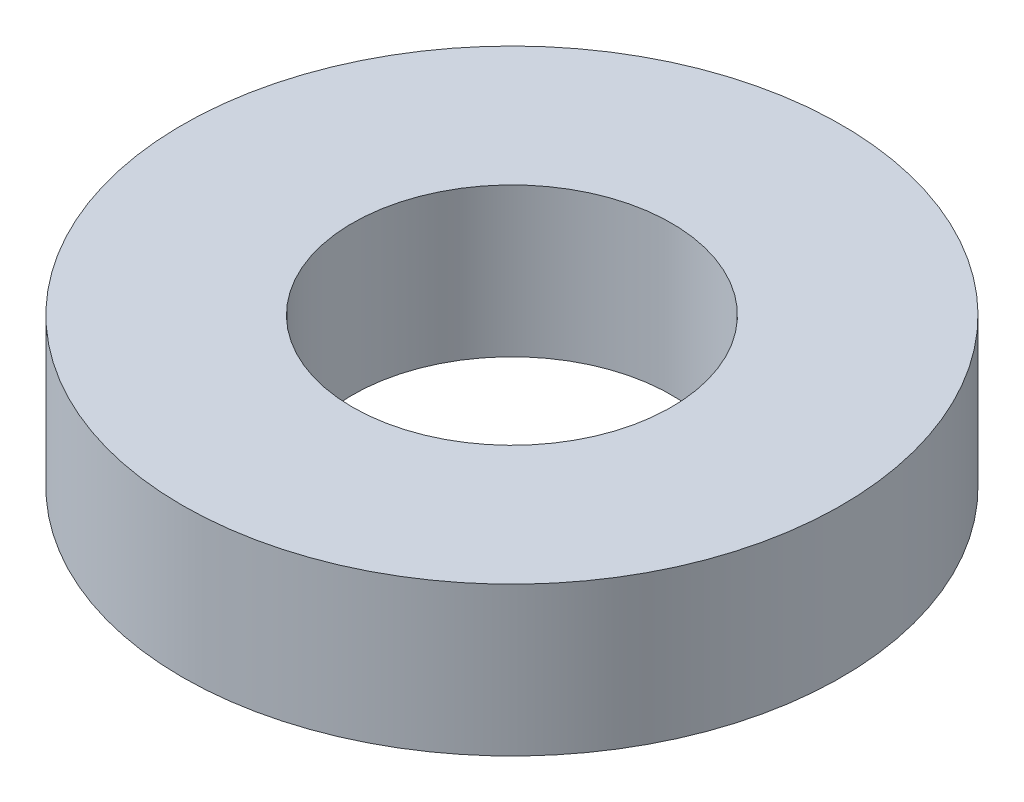
SolidWorks part; units mm, degrees
ref_plane "Front Plane" through (0, 0, 0) normal (0, 0, 1) x (1, 0, 0)
ref_plane "Top Plane" through (0, 0, 0) normal (0, 1, 0) x (1, 0, 0)
ref_plane "Right Plane" through (0, 0, 0) normal (1, 0, 0) x (0, 0, -1)
sketch "Sketch1" plane through (0, 0, 0) normal (0, 1, 0) x (1, 0, 0)
  circle A0 centre (0, 0) radius 3.75
  circle A1 centre (0, 0) radius 7.75
  dimension "D1" = 7.5
  dimension "D2" = 4
extrude "Boss-Extrude1" add sketch "Sketch1" along normal blind 3.5
